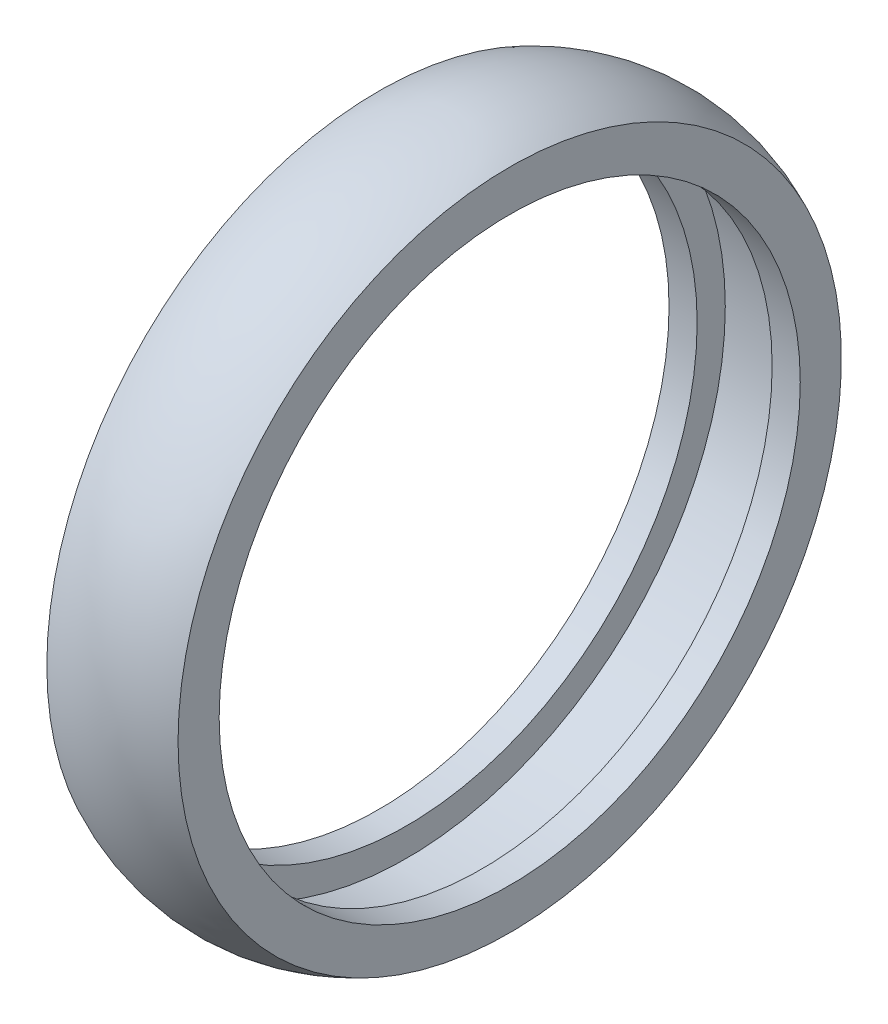
SolidWorks part; units mm, degrees
ref_plane "Front Plane" through (0, 0, 0) normal (0, 0, 1) x (1, 0, 0)
ref_plane "Top Plane" through (0, 0, 0) normal (0, 1, 0) x (1, 0, 0)
ref_plane "Right Plane" through (0, 0, 0) normal (1, 0, 0) x (0, 0, -1)
sketch "Sketch1" plane through (0, 0, 0) normal (0, 0, 1) x (1, 0, 0)
  line L0 (-690.4668, 0) -> (33832.8751, 0) construction
  line L1 (0, -690.4668) -> (0, 33832.8751) construction
  line L2 (4, 34) -> (-4, 34)
  line L3 (-4, 34) -> (-4, 31)
  line L4 (-4, 31) -> (-7, 31)
  line L5 (-7, 31) -> (-7, 35.3875)
  line L7 (7, 31) -> (7, 35.3875)
  line L8 (4, 31) -> (7, 31)
  line L9 (4, 34) -> (4, 31)
  arc A0 (-7, 35.3875) -> (7, 35.3875) centre (0, 21) cw
  dimension "D6" = 16
  dimension "D1" = 68
  dimension "D3" = 3
  dimension "D4" = 8
  dimension "D5" = 3
  dimension "D2" = 3
revolve "Revolve1" add sketch "Sketch1" angle 360 about L0
equation "\"width\"= 24"
equation "\"thk\"= 3"
equation "\"holesize\"= 4.2"
equation "\"holedistance\"= ( 20 + 12 ) / 2"
equation "\"threaded_hole\"= 3.9"
equation "\"fillet_radius\"= 2"
equation "\"ground_clearance\"= 25"
equation "\"tire_thk\"= 3"
equation "\"innerwheel_diam\" = \"wheel_diam\"-2*\"tire_thk\""
equation "\"innerwheel_thk\"= 8"
equation "\"wheel_diam\"= 2*(\"width\"/2+\"ground_clearance\")"
equation "\"D1@Sketch1\"=\"innerwheel_diam\""
equation "\"D3@Sketch1\"=\"D2@Sketch1\""
equation "\"D4@Sketch1\"=\"innerwheel_thk\""
equation "\"D2@Sketch1\"=\"tire_thk\""
equation "\"coloursensor_holesize\"= 2.65"
equation "\"hole_to_edge\" = 4"
